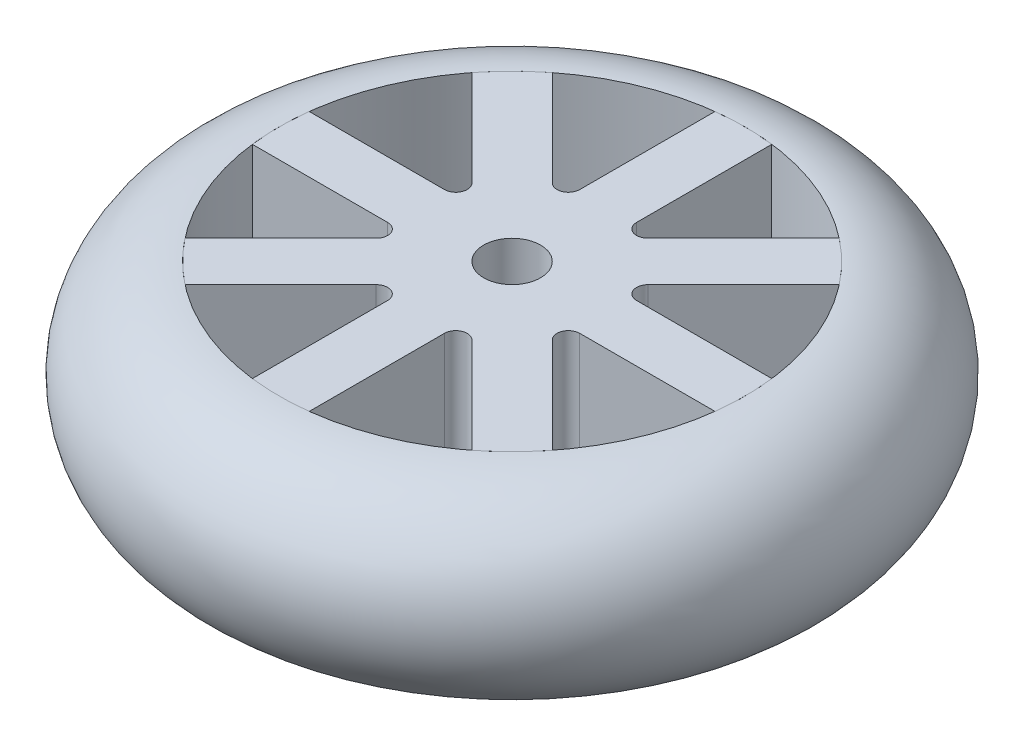
SolidWorks part; units mm, degrees
ref_plane "Front Plane" through (0, 0, 0) normal (0, 0, 1) x (1, 0, 0)
ref_plane "Top Plane" through (0, 0, 0) normal (0, 1, 0) x (1, 0, 0)
ref_plane "Right Plane" through (0, 0, 0) normal (1, 0, 0) x (0, 0, -1)
sketch "Sketch1" plane through (0, 0, 0) normal (0, 0, 1) x (1, 0, 0)
  line L0 (0, -19.41) -> (0, 44.218) construction
  line L1 (-20.5, 0) -> (-20.5, 17)
  arc A0 (-20.5, 17) -> (-20.5, 0) centre (-20.5, 8.5) ccw
  point P6 (-29, 8.5)
  dimension "D2" = 29
  dimension "D3" = 8.5
  dimension "D1" = 17
revolve "Revolve1" add sketch "Sketch1" angle 360 about L0
sketch "Sketch2" plane through (0, 0, 0) normal (0, 1, 0) x (1, 0, 0)
  circle A0 centre (0, 0) radius 7
  circle A1 centre (0, 0) radius 2.5
  dimension "D1" = 14
  dimension "D2" = 5
extrude "Boss-Extrude1" add sketch "Sketch2" along normal blind 17 separate body
sketch "Sketch3" plane through (0, 0, 0) normal (0, 1, 0) x (1, 0, 0)
  line L0 (0, -20.5) -> (0, 20.5) construction
  line L1 (-20.5, 0) -> (20.5, 0) construction
  line L2 (-14.4957, -14.4957) -> (14.4957, 14.4957) construction
  line L3 (-14.4957, 14.4957) -> (14.4957, -14.4957) construction
  line L4 (-2.5, 20.347) -> (-2.5, 8.4497)
  line L5 (2.5, 20.347) -> (2.5, 8.4497)
  line L6 (12.6197, 16.1553) -> (4.2071, 7.7426)
  line L7 (16.1553, 12.6197) -> (7.7426, 4.2071)
  line L8 (20.347, 2.5) -> (8.4497, 2.5)
  line L9 (20.347, -2.5) -> (8.4497, -2.5)
  line L10 (16.1553, -12.6197) -> (7.7426, -4.2071)
  line L11 (12.6197, -16.1553) -> (4.2071, -7.7426)
  line L12 (2.5, -20.347) -> (2.5, -8.4497)
  line L13 (-2.5, -20.347) -> (-2.5, -8.4497)
  line L14 (-12.6197, -16.1553) -> (-4.2071, -7.7426)
  line L15 (-16.1553, -12.6197) -> (-7.7426, -4.2071)
  line L16 (-20.347, -2.5) -> (-8.4497, -2.5)
  line L17 (-20.347, 2.5) -> (-8.4497, 2.5)
  line L18 (-16.1553, 12.6197) -> (-7.7426, 4.2071)
  line L19 (-12.6197, 16.1553) -> (-4.2071, 7.7426)
  circle A0 centre (0, 0) radius 20.5 construction
  arc A1 (-7.7426, 4.2071) -> (-8.4497, 2.5) centre (-8.4497, 3.5) cw
  arc A2 (-8.4497, -2.5) -> (-7.7426, -4.2071) centre (-8.4497, -3.5) cw
  arc A3 (-4.2071, -7.7426) -> (-2.5, -8.4497) centre (-3.5, -8.4497) cw
  arc A4 (2.5, -8.4497) -> (4.2071, -7.7426) centre (3.5, -8.4497) cw
  arc A5 (7.7426, -4.2071) -> (8.4497, -2.5) centre (8.4497, -3.5) cw
  arc A6 (8.4497, 2.5) -> (7.7426, 4.2071) centre (8.4497, 3.5) cw
  arc A7 (2.5, 8.4497) -> (4.2071, 7.7426) centre (3.5, 8.4497) ccw
  arc A8 (-2.5, 8.4497) -> (-4.2071, 7.7426) centre (-3.5, 8.4497) cw
  spline S0 degree 2 poles (-2.5, 20.347) (0, 20.653) (2.5, 20.347) knots 0 0 0 1 1 1
  spline S1 degree 2 poles (-16.1553, 12.6197) (-14.6039, 14.6039) (-12.6197, 16.1553) knots 0 0 0 1 1 1
  spline S2 degree 2 poles (-20.347, -2.5) (-20.653, 0) (-20.347, 2.5) knots 0 0 0 1 1 1
  spline S3 degree 2 poles (-16.1553, -12.6197) (-14.6039, -14.6039) (-12.6197, -16.1553) knots 0 0 0 1 1 1
  spline S4 degree 2 poles (-2.5, -20.347) (0, -20.653) (2.5, -20.347) knots 0 0 0 1 1 1
  spline S5 degree 2 poles (12.6197, -16.1553) (14.6039, -14.6039) (16.1553, -12.6197) knots 0 0 0 1 1 1
  spline S6 degree 2 poles (20.347, 2.5) (20.653, 0) (20.347, -2.5) knots 0 0 0 1 1 1
  spline S7 degree 2 poles (12.6197, 16.1553) (14.6039, 14.6039) (16.1553, 12.6197) knots 0 0 0 1 1 1
  point P11 (0, 0)
  point P12 (0, 0)
  dimension "D19" = 1
  dimension "D1" = 45
  dimension "D2" = 45
  dimension "D3" = 5
  dimension "D4" = 2.5
  dimension "D5" = 5
  dimension "D6" = 2.5
  dimension "D7" = 5
  dimension "D8" = 2.5
  dimension "D9" = 5
  dimension "D10" = 2.5
  dimension "D11" = 5
  dimension "D12" = 2.5
  dimension "D13" = 5
  dimension "D14" = 2.5
  dimension "D15" = 5
  dimension "D16" = 2.5
  dimension "D17" = 5
  dimension "D18" = 2.5
extrude "Boss-Extrude2" add sketch "Sketch3" along normal blind 17
sketch "Sketch4" plane through (0, 17, 0) normal (0, 1, 0) x (1, 0, 0)
  circle A1 centre (0, 0) radius 2.5
  dimension "D1" = 5
extrude "Cut-Extrude1" cut sketch "Sketch4" against normal blind 17
